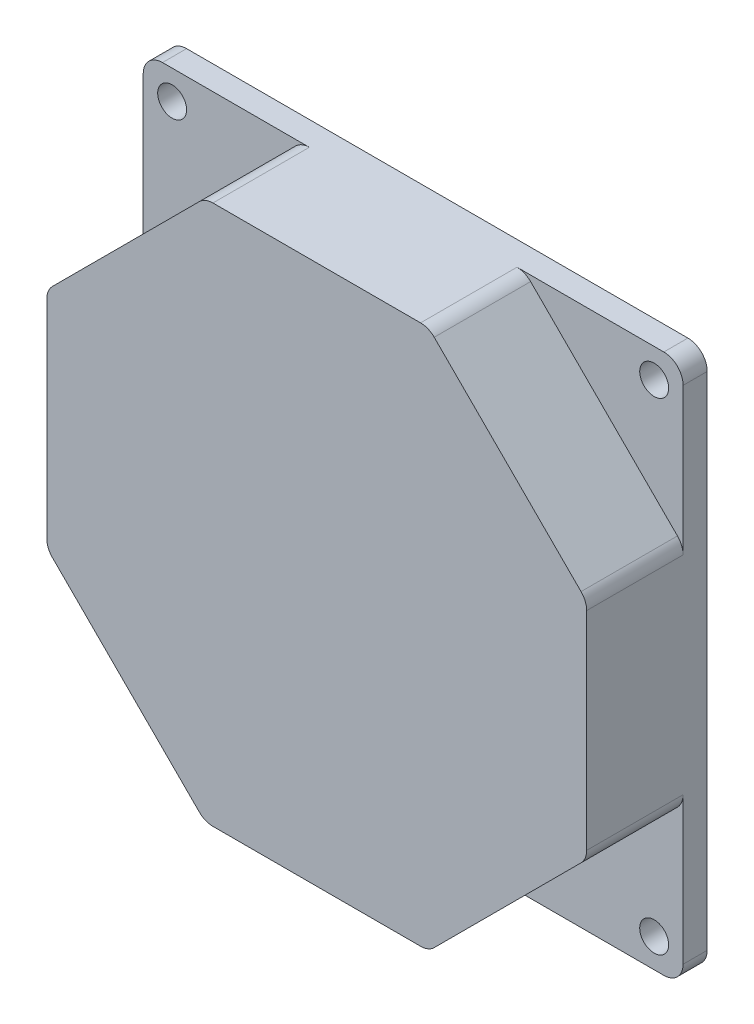
SolidWorks part; units mm, degrees
material "6061 Alloy"
ref_plane "Front Plane" through (0, 0, 0) normal (0, 0, 1) x (1, 0, 0)
ref_plane "Top Plane" through (0, 0, 0) normal (0, 1, 0) x (1, 0, 0)
ref_plane "Right Plane" through (0, 0, 0) normal (1, 0, 0) x (0, 0, -1)
sketch "Sketch1" plane through (0, 0, 0) normal (0, 0, 1) x (1, 0, 0)
  line L1 (-26, 28) -> (26, 28)
  line L2 (-28, 26) -> (-28, -26)
  line L3 (-26, -28) -> (26, -28)
  line L4 (28, 26) -> (28, -26)
  line L5 (-28, 28) -> (28, -28) construction
  line L6 (-28, -28) -> (28, 28) construction
  circle A0 centre (-25, 25) radius 1.5
  arc A1 (-28, -26) -> (-26, -28) centre (-26, -26) ccw
  arc A2 (26, -28) -> (28, -26) centre (26, -26) ccw
  arc A3 (28, 26) -> (26, 28) centre (26, 26) ccw
  arc A4 (-28, 26) -> (-26, 28) centre (-26, 26) cw
  circle A5 centre (25, 25) radius 1.5
  circle A6 centre (25, -25) radius 1.5
  circle A7 centre (-25, -25) radius 1.5
  point P0 (0, 0)
  point P20 (24.4103, 21.1034)
  point P21 (0, 0)
  point P22 (0, 0)
  point P29 (0, 0)
  dimension "D3" = 25
  dimension "D4" = 3
  dimension "D5" = 2
  dimension "D1" = 56
  dimension "D2" = 56
  dimension "D6" = 4
extrude "Boss-Extrude1" add sketch "Sketch1" along normal blind 2.5
sketch "Sketch2" plane through (0, 0, 2.5) normal (0, 0, 1) x (1, 0, 0)
  line L0 (-11.598, -28) -> (11.598, -28)
  line L1 (28, -11.598) -> (28, 11.598)
  line L2 (28, 11.598) -> (11.598, 28)
  line L3 (11.598, 28) -> (-11.598, 28)
  line L4 (-11.598, 28) -> (-28, 11.598)
  line L5 (-28, 11.598) -> (-28, -11.598)
  line L6 (-28, -11.598) -> (-11.598, -28)
  line L7 (11.598, -28) -> (28, -11.598)
  line L8 (26, 28) -> (-26, 28) construction
  circle A0 centre (0, 0) radius 28 construction
extrude "Boss-Extrude2" add sketch "Sketch2" along normal blind 10
fillet "Fillet1" radius 2 8 edges at (28, -11.598, 7.5) (11.598, -28, 7.5) (-11.598, -28, 7.5) (-28, -11.598, 7.5) (-28, 11.598, 7.5) (-11.598, 28, 7.5) (11.598, 28, 7.5) (28, 11.598, 7.5)
sketch "Sketch3" plane through (0, 0, 0) normal (0, 0, -1) x (-1, 0, 0)
  circle A0 centre (0, 0) radius 2.5
  dimension "D1" = 5
extrude "Cut-Extrude1" cut sketch "Sketch3" against normal blind 5
sketch "Sketch4" plane through (0, 0, 0) normal (0, 0, -1) x (-1, 0, 0)
  circle A0 centre (0, 0) radius 4.5
  circle A1 centre (0, 0) radius 5
  dimension "D1" = 9
  dimension "D2" = 10
extrude "Cut-Extrude2" cut sketch "Sketch4" against normal blind 0.5
sketch "Sketch5" plane through (0, -28, 0) normal (0, -1, 0) x (1, 0, 0)
  line L0 (-10.7696, 12.5) -> (10.7696, 12.5) construction
  line L1 (-5, 10.5) -> (5, 10.5)
  line L2 (-5, 10.5) -> (-5, 4.5)
  line L3 (-5, 4.5) -> (5, 4.5)
  line L4 (5, 10.5) -> (5, 4.5)
  line L5 (-3, 7.5) -> (3, 7.5) construction
  circle A0 centre (-3, 7.5) radius 0.5
  circle A1 centre (-1, 7.5) radius 0.5
  circle A2 centre (1, 7.5) radius 0.5
  circle A3 centre (3, 7.5) radius 0.5
  point P15 (-1.0489, 7.0605)
  point P16 (0, 0)
  point P17 (0, 0)
  dimension "D5" = 3
  dimension "D7" = 1
  dimension "D8" = 2
  dimension "D11" = 1
  dimension "D12" = 1
  dimension "D13" = 1
  dimension "D1" = 2
  dimension "D2" = 5
  dimension "D3" = 10
  dimension "D4" = 6
  dimension "D6" = 2
  dimension "D9" = 2
  dimension "D10" = 2
extrude "Cut-Extrude3" cut sketch "Sketch5" against normal blind 5
